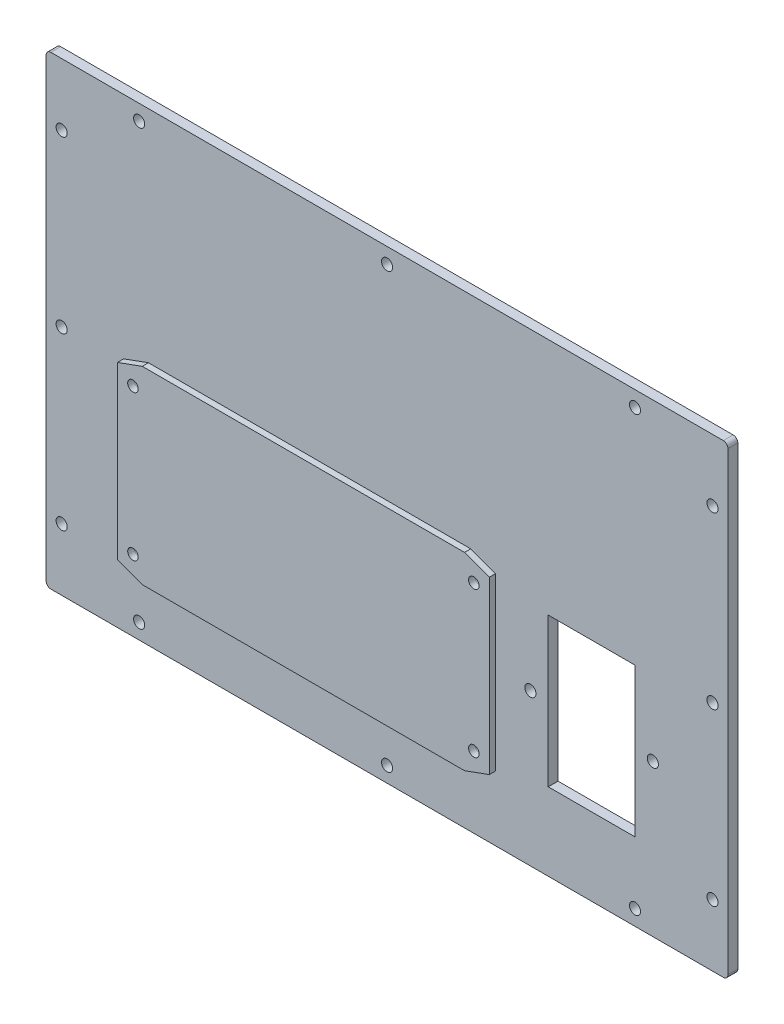
SolidWorks part; units mm, degrees
ref_plane "Front Plane" through (0, 0, 0) normal (0, 0, 1) x (1, 0, 0)
ref_plane "Top Plane" through (0, 0, 0) normal (0, 1, 0) x (1, 0, 0)
ref_plane "Right Plane" through (0, 0, 0) normal (1, 0, 0) x (0, 0, -1)
sketch "Sketch1" plane through (0, 0, 0) normal (0, 0, 1) x (1, 0, 0)
  line L0 (0, 0) -> (0, 75) construction
  line L1 (-110, -75) -> (110, -75)
  line L2 (-110, -75) -> (-110, 75)
  line L3 (-110, 75) -> (110, 75)
  line L4 (110, -75) -> (110, 75)
  line L5 (-110, -75) -> (110, 75) construction
  line L6 (-110, 75) -> (110, -75) construction
  line L15 (0, 0) -> (-110, 0) construction
  point P0 (0, 0)
  dimension "D1" = 220
  dimension "D2" = 150
extrude "Boss-Extrude1" add sketch "Sketch1" along normal blind 3.175
hole_wizard "M3 Clearance Hole1" positions "Sketch2" profile "Sketch3" hole size "M3" standard "ANSI Metric" end condition through all
sketch "Sketch2" plane through (0, 0, 3.175) normal (0, 0, 1) x (1, 0, 0)
  line L1 (-105, -70) -> (105, -70)
  line L2 (-105, -70) -> (-105, 70)
  line L3 (-105, 70) -> (105, 70)
  line L4 (105, -70) -> (105, 70)
  line L5 (-105, -70) -> (105, 70) construction
  line L6 (-105, 70) -> (105, -70) construction
  line L7 (-110, -75) -> (-110, 75) construction
  line L8 (-110, 75) -> (110, 75) construction
  point P2 (0, 0)
  point P113 (-80, 70)
  point P115 (80, 70)
  point P116 (0, 70)
  point P118 (-105, 55)
  point P120 (-105, 0)
  point P122 (-105, -55)
  point P124 (-80, -70)
  point P126 (0, -70)
  point P128 (80, -70)
  point P130 (105, -55)
  point P132 (105, 0)
  point P134 (105, 55)
  dimension "D1" = 5
  dimension "D2" = 5
  dimension "D3" = 80
  dimension "D4" = 80
  dimension "D5" = 55
  dimension "D6" = 55
sketch "Sketch3" plane through (0, 0, 3.175) normal (1, 0, 0) x (0, -1, 0)
  line L0 (0, 0) -> (0, 3.175)
  line L1 (0, 3.175) -> (1.8, 3.175)
  line L2 (1.8, 3.175) -> (1.8, 0)
  line L5 (1.8, 0) -> (0, 0)
  line L11 (0, -6.35) -> (0, 107.95) construction
  dimension "Thru Hole Dia." = 3.6
  dimension "Thru Hole Depth" = 3.175
sketch "Sketch4" plane through (0, 0, 3.175) normal (0, 0, 1) x (1, 0, 0)
  line L1 (-5, -5) -> (5, -5)
  line L2 (-5, -5) -> (-5, 5)
  line L3 (-5, 5) -> (5, 5)
  line L4 (5, -5) -> (5, 5)
  line L5 (-5, -5) -> (5, 5) construction
  line L6 (-5, 5) -> (5, -5) construction
  point P0 (0, 0)
  dimension "D1" = 10
  dimension "D2" = 10
extrude "Boss-Extrude2" add sketch "Sketch4" against normal through all
fillet "Fillet2" radius 1.5 4 edges at (-110, -75, 1.5875) (110, -75, 1.5875) (110, 75, 1.5875) (-110, 75, 1.5875)
sketch "Sketch5" plane through (0, 0, 3.175) normal (0, 0, 1) x (1, 0, 0)
  line L0 (46.25, -26) -> (85.75, -26) construction
  line L1 (52, -50) -> (80, -50)
  line L2 (52, -50) -> (52, -2)
  line L3 (52, -2) -> (80, -2)
  line L4 (80, -50) -> (80, -2)
  line L5 (52, -50) -> (80, -2) construction
  line L6 (52, -2) -> (80, -50) construction
  line L7 (-108.5, -75) -> (108.5, -75) construction
  line L8 (110, -73.5) -> (110, 73.5) construction
  line L10 (-90, -60) -> (30, -60)
  line L11 (-90, -60) -> (-90, 60)
  line L12 (-90, 60) -> (30, 60)
  line L13 (30, -60) -> (30, 60)
  line L14 (-90, -60) -> (30, 60) construction
  line L15 (-90, 60) -> (30, -60) construction
  line L16 (-110, -73.5) -> (-110, 73.5) construction
  point P0 (66, -26)
  point P8 (66, -26)
  point P12 (-30, 0)
  dimension "D1" = 28
  dimension "D2" = 48
  dimension "D3" = 39.5
  dimension "D4" = 25
  dimension "D5" = 30
  dimension "D6" = 120
  dimension "D7" = 120
  dimension "D8" = 15
  dimension "D9" = 20
extrude "Cut-Extrude1" cut sketch "Sketch5" against normal through all contours L1 L4 L3 L2 | L11 L10 L13 L12
hole_wizard "M3 Clearance Hole2" positions "Sketch6" profile "Sketch7" hole size "M3" standard "ANSI Metric" end condition through all
sketch "Sketch6" plane through (0, 0, 3.175) normal (0, 0, 1) x (1, 0, 0)
  point P0 (46.25, -26)
  point P3 (85.75, -26)
sketch "Sketch7" plane through (46.25, -26, 3.175) normal (1, 0, 0) x (0, -1, 0)
  line L0 (0, 0) -> (0, 3.175)
  line L1 (0, 3.175) -> (1.8, 3.175)
  line L2 (1.8, 3.175) -> (1.8, 0)
  line L5 (1.8, 0) -> (0, 0)
  line L11 (0, -6.35) -> (0, 107.95) construction
  dimension "Thru Hole Dia." = 3.6
  dimension "Thru Hole Depth" = 3.175
sketch "Sketch8" plane through (0, 0, 3.175) normal (0, 0, 1) x (1, 0, 0)
  line L0 (-110, -73.5) -> (-110, 73.5) construction
  line L1 (-75, 2) -> (25, 2)
  line L2 (-75, 2) -> (-75, -55)
  line L3 (-75, -55) -> (25, -55)
  line L4 (25, 2) -> (25, -55)
  line L5 (-108.5, -75) -> (108.5, -75) construction
  dimension "D1" = 57
  dimension "D2" = 100
  dimension "D3" = 35
  dimension "D4" = 20
extrude "Cut-Extrude2" cut sketch "Sketch8" against normal through all
hole_wizard "M3 Clearance Hole3" positions "Sketch9" profile "Sketch10" hole size "M3" standard "ANSI Metric" end condition through all
sketch "Sketch9" plane through (0, 0, 3.175) normal (0, 0, 1) x (1, 0, 0)
  line L0 (-80, -3) -> (-80, -50) construction
  line L2 (30, -3) -> (30, -50) construction
  line L4 (-75, 2) -> (-75, -55) construction
  line L5 (25, -55) -> (25, 2) construction
  line L6 (25, 2) -> (-75, 2) construction
  point P0 (-80, -3)
  point P2 (-80, -50)
  point P4 (30, -50)
  point P6 (30, -3)
  point P21 (-80, -26.5)
  point P24 (-75, -26.5)
  dimension "D1" = 5
  dimension "D2" = 5
  dimension "D3" = 5
sketch "Sketch10" plane through (-80, -3, 3.175) normal (1, 0, 0) x (0, -1, 0)
  line L0 (0, 0) -> (0, 3.175)
  line L1 (0, 3.175) -> (1.7, 3.175)
  line L2 (1.7, 3.175) -> (1.7, 0)
  line L5 (1.7, 0) -> (0, 0)
  line L11 (0, -6.35) -> (0, 107.95) construction
  dimension "Thru Hole Dia." = 3.4
  dimension "Thru Hole Depth" = 3.175
sketch "Sketch11" plane through (0, 0, 3.175) normal (0, 0, 1) x (1, 0, 0)
  line L0 (35, -54.0882) -> (27, -57)
  line L1 (35, 1.0882) -> (35, -54.0882)
  line L2 (27, 4) -> (35, 1.0882)
  line L10 (-77, 4) -> (-85, 1.0882)
  line L11 (-85, 1.0882) -> (-85, -54.0882)
  line L12 (-85, -54.0882) -> (-77, -57)
  line L13 (-25, 4) -> (-25, -57) construction
  line L14 (27, -57) -> (27, 4)
  line L15 (-77, -57) -> (27, -57)
  line L16 (-77, 4) -> (-77, -57)
  line L17 (27, 4) -> (-77, 4)
  line L18 (27, -57) -> (27, 4)
  line L19 (-77, -57) -> (27, -57)
  line L20 (-77, 4) -> (-77, -57)
  line L21 (27, 4) -> (-77, 4)
  circle M9 centre (-80, -3) radius 1.7
  circle M10 centre (-80, -50) radius 1.7
  circle M11 centre (30, -50) radius 1.7
  circle M12 centre (30, -3) radius 1.7
  line M13 (-75, -55) -> (-75, 2)
  line M14 (-75, 2) -> (25, 2)
  line M15 (25, 2) -> (25, -55)
  line M16 (25, -55) -> (-75, -55)
  dimension "D2" = 8
  dimension "D3" = 70
  dimension "D1" = 2
extrude "Boss-Extrude3" add sketch "Sketch11" along normal blind 2 separate body contours L20 L10 L11 L12 M9 M10 | L13 L21 L20 L19 M16 M13 M14 | L13 M14 M13 M16 | L13 M14 M16 M15 | L21 L13 L19 L18 M14 M15 M16 | L18 L0 L1 L2 M12 M11
sketch "Sketch12" plane through (0, 0, 3.175) normal (0, 0, -1) x (-1, 0, 0)
  line L14 (-24, -54) -> (74, -54)
  line L15 (74, -54) -> (74, 1)
  line L16 (-24, 1) -> (-24, -54)
  line L17 (74, 1) -> (-24, 1)
  line L18 (-24, -54) -> (74, -54)
  line L19 (74, -54) -> (74, 1)
  line L20 (-24, 1) -> (-24, -54)
  line L21 (74, 1) -> (-24, 1)
  dimension "D1" = 1
extrude "Boss-Extrude5" add sketch "Sketch12" along normal blind 2 separate body
